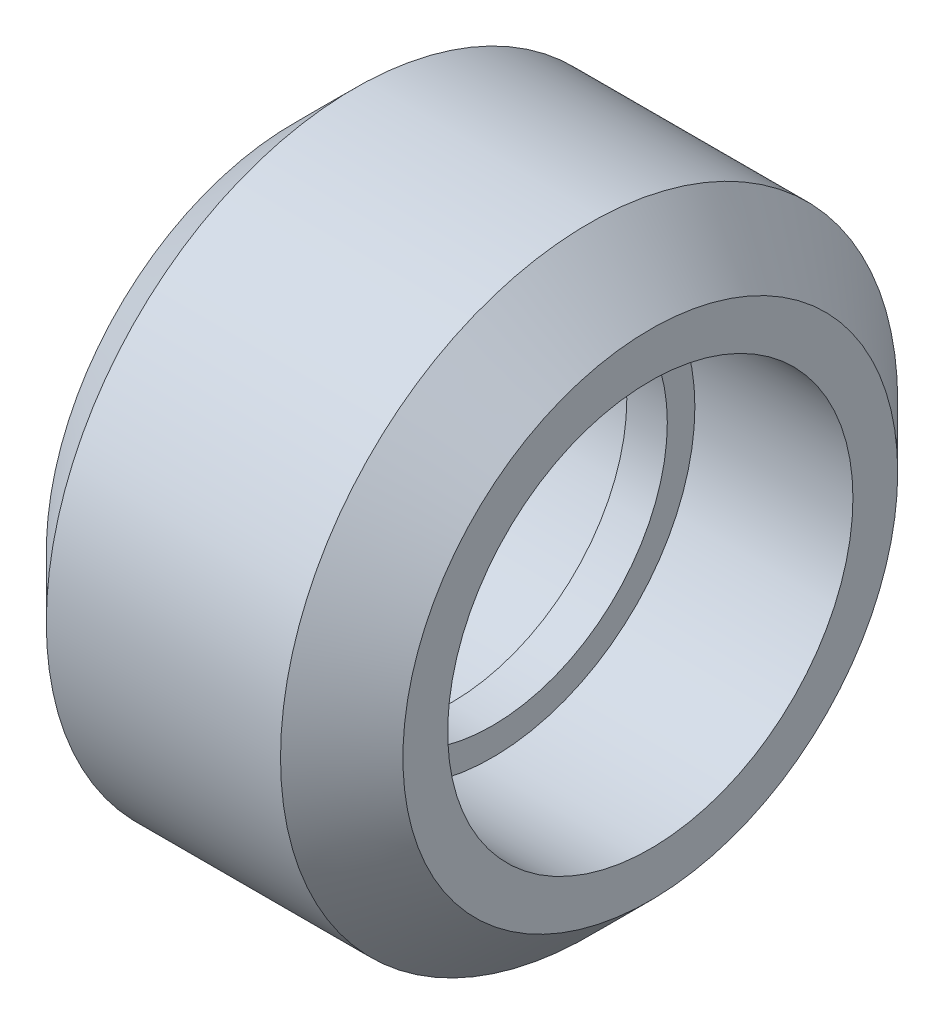
SolidWorks part; units mm, degrees
material "Delrin 2700 NC010, Low Viscosity Acetal Copolymer (SS)"
ref_plane "Front Plane" through (0, 0, 0) normal (0, 0, 1) x (1, 0, 0)
ref_plane "Top Plane" through (0, 0, 0) normal (0, 1, 0) x (1, 0, 0)
ref_plane "Right Plane" through (0, 0, 0) normal (1, 0, 0) x (0, 0, -1)
sketch "Sketch1" plane through (0, 0, 0) normal (0, 0, 1) x (1, 0, 0)
  line L0 (0.5, 4.32) -> (-0.5, 4.32)
  line L1 (-0.5, 4.32) -> (-0.5, 5)
  line L2 (-0.5, 5) -> (-4.4, 5)
  line L3 (-4.4, 5) -> (-4.4, 6.105)
  line L4 (-4.4, 6.105) -> (-2.89, 7.615)
  line L5 (-2.89, 7.615) -> (2.89, 7.615)
  line L6 (0, 7.615) -> (0, 4.32) construction
  line L7 (4.4, 6.105) -> (2.89, 7.615)
  line L8 (4.4, 5) -> (4.4, 6.105)
  line L9 (0.5, 5) -> (4.4, 5)
  line L10 (0.5, 4.32) -> (0.5, 5)
  line L11 (0, 0) -> (-12.6359, 0) construction
  dimension "D1" = 12.21
  dimension "8.64" = 8.64
  dimension "D2" = 10
  dimension "D3" = 15.23
  dimension "D4" = 1
  dimension "D5" = 45
  dimension "D6" = 8.8
  dimension "D7" = 5.78
revolve "Revolve1" add sketch "Sketch1" angle 360 about L11
ref_plane "Plane1" through (0, 0, 0) normal (1, 0, 0) x (0, 0, -1)
